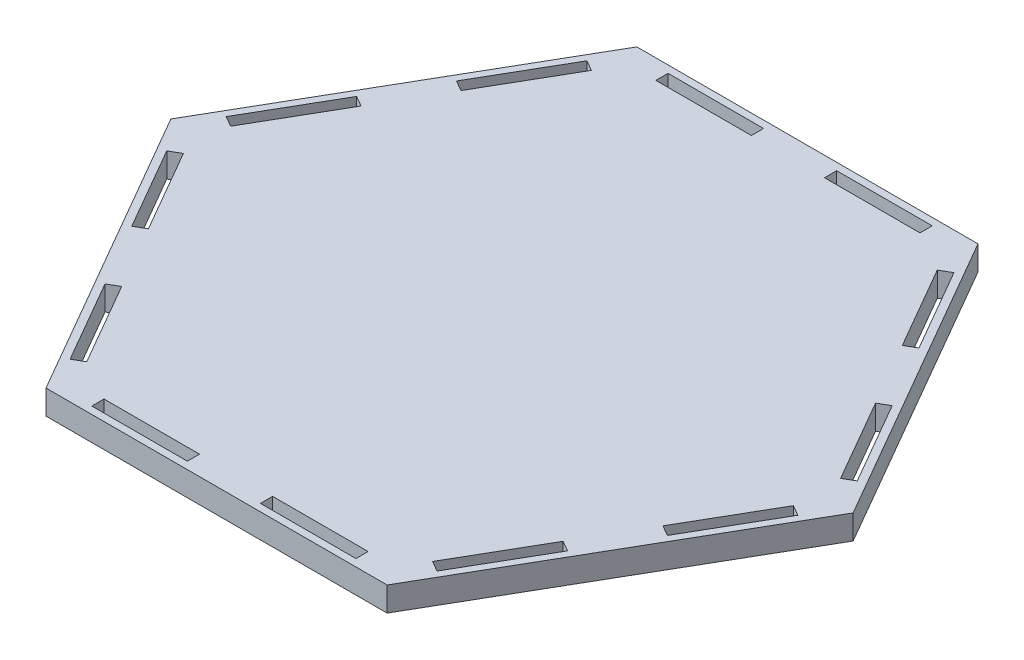
SolidWorks part; units mm, degrees
material "Cedar"
ref_plane "Front Plane" through (0, 0, 0) normal (0, 0, 1) x (1, 0, 0)
ref_plane "Top Plane" through (0, 0, 0) normal (0, 1, 0) x (1, 0, 0)
ref_plane "Right Plane" through (0, 0, 0) normal (1, 0, 0) x (0, 0, -1)
sketch "Sketch1" plane through (0, 0, 0) normal (0, 1, 0) x (1, 0, 0)
  line L0 (-88.9, 0) -> (-44.45, -76.9897)
  line L1 (88.9, 0) -> (44.45, 76.9897)
  line L2 (44.45, 76.9897) -> (-44.45, 76.9897)
  line L3 (-44.45, 76.9897) -> (-88.9, 0)
  line L4 (-44.45, -76.9897) -> (44.45, -76.9897)
  line L5 (44.45, -76.9897) -> (88.9, 0)
  line L6 (0, 0) -> (88.9, 0) construction
  circle A0 centre (0, 0) radius 76.9897 construction
  dimension "D1" = 88.9
extrude "Boss-Extrude1" add sketch "Sketch1" along normal blind 6.35
sketch "Sketch2" plane through (0, 6.35, 0) normal (0, 1, 0) x (1, 0, 0)
  line L0 (0, 0) -> (0, 58.6588) construction
  line L1 (50.8, -29.3294) -> (0, 58.6588) construction
  line L2 (0, 58.6588) -> (-50.8, -29.3294) construction
  line L3 (-50.8, -29.3294) -> (50.8, -29.3294) construction
  line L4 (-85.9671, 5.08) -> (-38.5841, -76.9897) construction
  line L5 (-44.45, 76.9897) -> (-88.9, 0) construction
  line L6 (-44.45, -76.9897) -> (44.45, -76.9897) construction
  line L7 (-88.9, 0) -> (-44.45, -76.9897) construction
  line L8 (-66.675, -38.4948) -> (-62.2756, -35.9548) construction
  line L9 (-79.4841, -6.1488) -> (-82.2337, -7.7363)
  line L10 (-82.2337, -7.7363) -> (-69.7877, -29.2934)
  line L11 (-69.7877, -29.2934) -> (-67.0381, -27.7059)
  line L12 (-67.0381, -27.7059) -> (-79.4841, -6.1488)
  line L13 (-45.0671, -65.7608) -> (-47.8167, -67.3483)
  line L14 (-57.5131, -44.2037) -> (-45.0671, -65.7608)
  line L15 (-47.8167, -67.3483) -> (-60.2627, -45.7912)
  line L16 (-60.2627, -45.7912) -> (-57.5131, -44.2037)
  line L17 (-38.5841, 76.9897) -> (-85.9671, -5.08) construction
  line L18 (-45.0671, 65.7608) -> (-47.8167, 67.3483)
  line L19 (-47.8167, 67.3483) -> (-60.2627, 45.7912)
  line L20 (-57.5131, 44.2037) -> (-45.0671, 65.7608)
  line L21 (-60.2627, 45.7912) -> (-57.5131, 44.2037)
  line L22 (-66.675, 38.4948) -> (-62.2756, 35.9548) construction
  line L23 (-69.7877, 29.2934) -> (-67.0381, 27.7059)
  line L24 (-82.2337, 7.7363) -> (-69.7877, 29.2934)
  line L25 (-67.0381, 27.7059) -> (-79.4841, 6.1488)
  line L26 (-79.4841, 6.1488) -> (-82.2337, 7.7363)
  line L27 (47.3829, 71.9097) -> (-47.3829, 71.9097) construction
  line L28 (34.417, 71.9097) -> (34.417, 75.0847)
  line L29 (34.417, 75.0847) -> (9.525, 75.0847)
  line L30 (9.525, 71.9097) -> (34.417, 71.9097)
  line L31 (9.525, 75.0847) -> (9.525, 71.9097)
  line L32 (0, 76.9897) -> (0, 71.9097) construction
  line L33 (-9.525, 75.0847) -> (-9.525, 71.9097)
  line L34 (-34.417, 75.0847) -> (-9.525, 75.0847)
  line L35 (-9.525, 71.9097) -> (-34.417, 71.9097)
  line L36 (-34.417, 71.9097) -> (-34.417, 75.0847)
  line L37 (85.9671, -5.08) -> (38.5841, 76.9897) construction
  line L38 (79.4841, 6.1488) -> (82.2337, 7.7363)
  line L39 (82.2337, 7.7363) -> (69.7877, 29.2934)
  line L40 (67.0381, 27.7059) -> (79.4841, 6.1488)
  line L41 (69.7877, 29.2934) -> (67.0381, 27.7059)
  line L42 (66.675, 38.4948) -> (62.2756, 35.9548) construction
  line L43 (60.2627, 45.7912) -> (57.5131, 44.2037)
  line L44 (47.8167, 67.3483) -> (60.2627, 45.7912)
  line L45 (57.5131, 44.2037) -> (45.0671, 65.7608)
  line L46 (45.0671, 65.7608) -> (47.8167, 67.3483)
  line L47 (38.5841, -76.9897) -> (85.9671, 5.08) construction
  line L48 (45.0671, -65.7608) -> (47.8167, -67.3483)
  line L49 (47.8167, -67.3483) -> (60.2627, -45.7912)
  line L50 (57.5131, -44.2037) -> (45.0671, -65.7608)
  line L51 (60.2627, -45.7912) -> (57.5131, -44.2037)
  line L52 (66.675, -38.4948) -> (62.2756, -35.9548) construction
  line L53 (69.7877, -29.2934) -> (67.0381, -27.7059)
  line L54 (82.2337, -7.7363) -> (69.7877, -29.2934)
  line L55 (67.0381, -27.7059) -> (79.4841, -6.1488)
  line L56 (79.4841, -6.1488) -> (82.2337, -7.7363)
  line L57 (-47.3829, -71.9097) -> (47.3829, -71.9097) construction
  line L58 (-34.417, -71.9097) -> (-34.417, -75.0847)
  line L59 (-34.417, -75.0847) -> (-9.525, -75.0847)
  line L60 (-9.525, -71.9097) -> (-34.417, -71.9097)
  line L61 (-9.525, -75.0847) -> (-9.525, -71.9097)
  line L62 (0, -76.9897) -> (0, -71.9097) construction
  line L63 (9.525, -75.0847) -> (9.525, -71.9097)
  line L64 (34.417, -75.0847) -> (9.525, -75.0847)
  line L65 (9.525, -71.9097) -> (34.417, -71.9097)
  line L66 (34.417, -71.9097) -> (34.417, -75.0847)
  circle A0 centre (0, 0) radius 29.3294 construction
  point P13 (0, 0)
  point P92 (0, 0)
  point P94 (0, 0)
  dimension "D1" = 101.6
  dimension "D4" = 5.08
  dimension "D5" = 3.175
  dimension "D6" = 24.892
  dimension "D7" = 9.525
  dimension "D8" = 6
extrude "Cut-Extrude1" cut sketch "Sketch2" against normal through all
